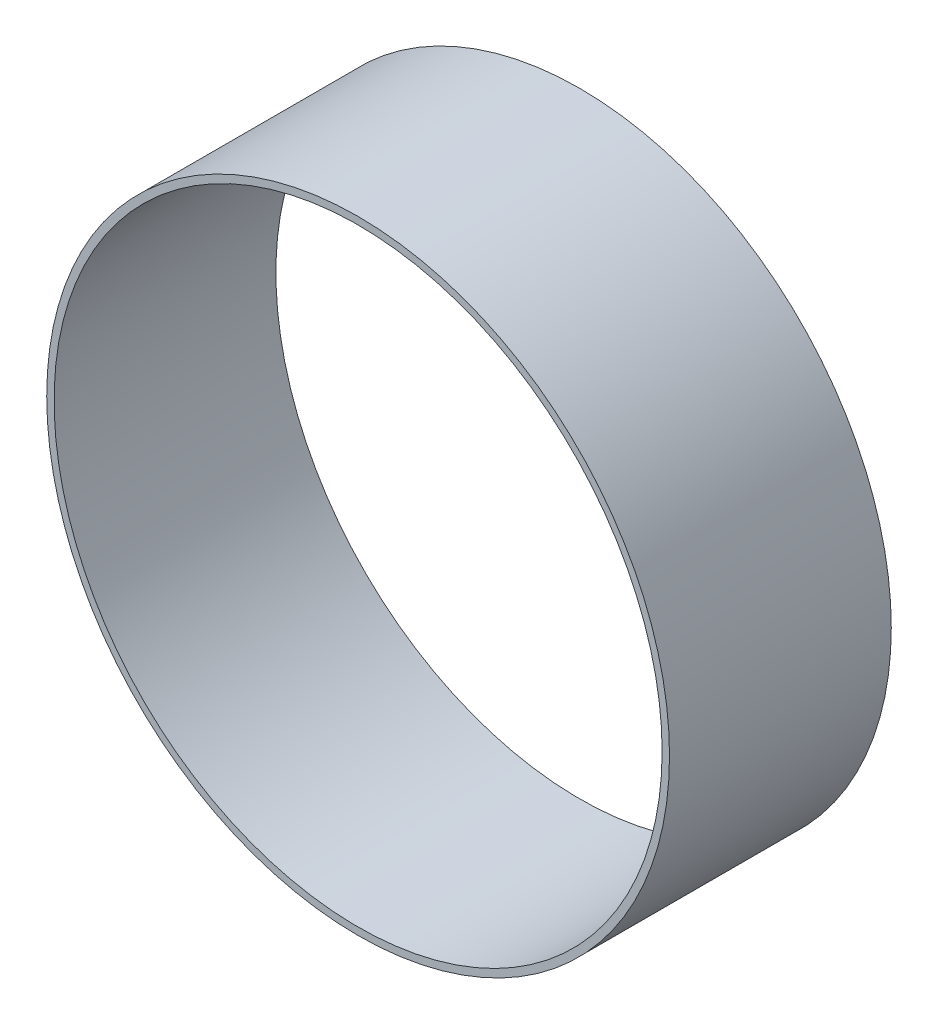
SolidWorks part; units mm, degrees
material "3.0205 (EN-AW 1200)"
ref_plane "Alzado" through (0, 0, 0) normal (0, 0, 1) x (1, 0, 0)
ref_plane "Planta" through (0, 0, 0) normal (0, 1, 0) x (1, 0, 0)
ref_plane "Vista lateral" through (0, 0, 0) normal (1, 0, 0) x (0, 0, -1)
sketch "Croquis1" plane through (0, 0, 0) normal (0, 0, 1) x (1, 0, 0)
  circle A0 centre (0, 0) radius 8.425
  circle A1 centre (0, 0) radius 8.225
  dimension "D1" = 16.85
  dimension "D2" = 0.2
extrude "Saliente-Extruir1" add sketch "Croquis1" along normal blind 6
